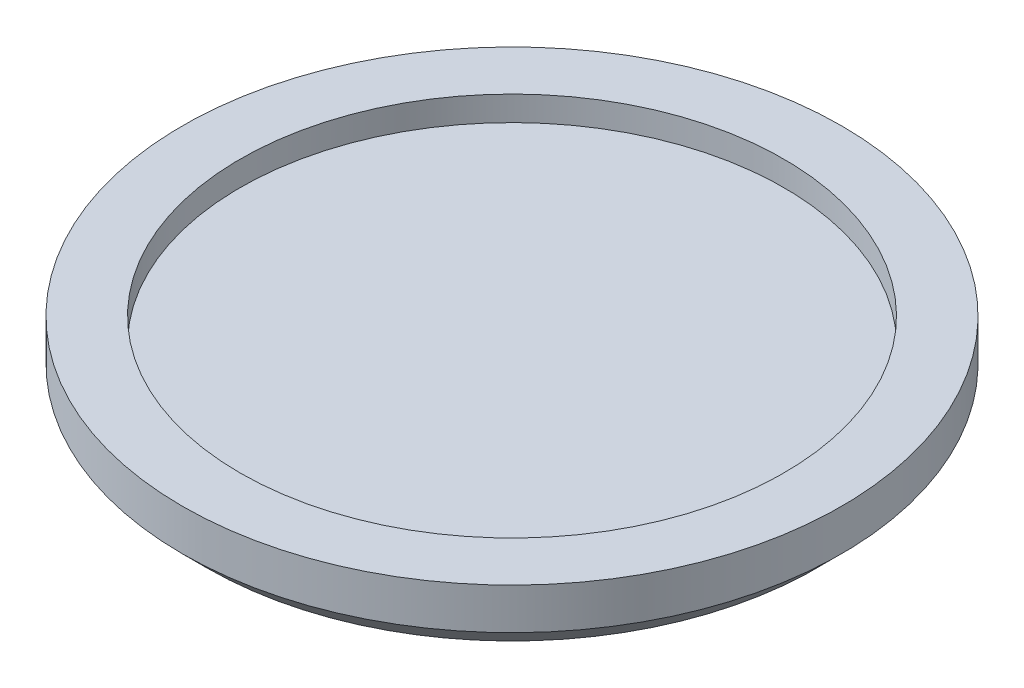
SolidWorks part; units mm, degrees
ref_plane "Front" through (0, 0, 0) normal (0, 0, 1) x (1, 0, 0)
ref_plane "Top" through (0, 0, 0) normal (0, 1, 0) x (1, 0, 0)
ref_plane "Right" through (0, 0, 0) normal (1, 0, 0) x (0, 0, -1)
sketch "Sketch1" plane through (0, 0, 0) normal (0, 1, 0) x (1, 0, 0)
  circle A0 centre (0, 0) radius 20
  dimension "D1" = 40
extrude "Boss-Extrude1" add sketch "Sketch1" along normal blind 4
sketch "Sketch2" plane through (0, 4, 0) normal (0, 1, 0) x (1, 0, 0)
  circle A0 centre (0, 0) radius 16.5
  dimension "D1" = 33
extrude "Cut-Extrude1" cut sketch "Sketch2" against normal blind 1.5
chamfer "Chamfer1" distance 1.5 angle 45 1 edges at (0, 0, 20)
